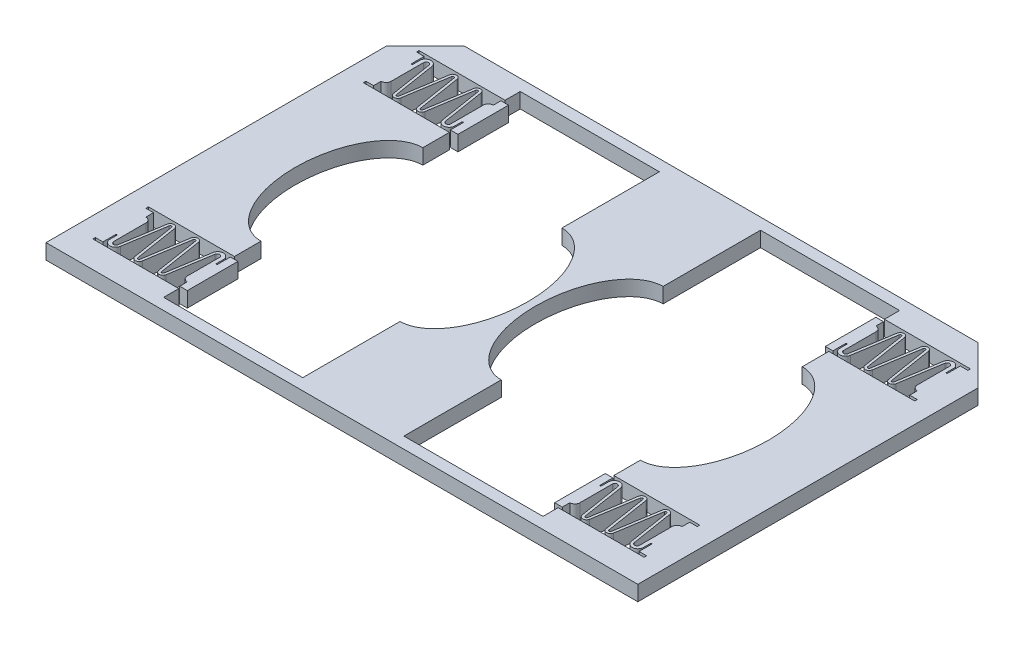
SolidWorks part; units mm, degrees
ref_plane "Front Plane" through (0, 0, 0) normal (0, 0, 1) x (1, 0, 0)
ref_plane "Top Plane" through (0, 0, 0) normal (0, 1, 0) x (1, 0, 0)
ref_plane "Right Plane" through (0, 0, 0) normal (1, 0, 0) x (0, 0, -1)
sketch "Sketch1" plane through (0, 0, 0) normal (0, 1, 0) x (1, 0, 0)
  line L0 (0, 67.25) -> (0, 0)
  line L1 (0, 0) -> (117, 0)
  line L2 (117, 0) -> (117, 67.25)
  line L3 (117, 67.25) -> (109.25, 75)
  line L4 (109.25, 75) -> (7.75, 75)
  line L5 (7.75, 75) -> (0, 67.25)
  line L6 (58.5, 0) -> (58.5, 75) construction
  line L7 (48.5, 2.25) -> (48.5, 0) construction
  line L8 (21, 72.75) -> (48.5, 72.75)
  line L9 (21, 72.75) -> (21, 2.25)
  line L10 (21, 2.25) -> (48.5, 2.25)
  line L11 (48.5, 72.75) -> (48.5, 2.25)
  line L12 (48.5, 72.75) -> (48.5, 75) construction
  line L13 (68.5, 72.75) -> (68.5, 2.25)
  line L14 (96, 2.25) -> (68.5, 2.25)
  line L15 (96, 72.75) -> (96, 2.25)
  line L16 (96, 72.75) -> (68.5, 72.75)
  dimension "D1" = 75
  dimension "D2" = 135
  dimension "D3" = 117
  dimension "D4" = 101.5
  dimension "D5" = 10
  dimension "D6" = 70.5
  dimension "D7" = 27.5
extrude "Boss-Extrude1" add sketch "Sketch1" along normal blind 3
sketch "Sketch3" plane through (0, 3, 0) normal (0, 1, 0) x (1, 0, 0)
  line L0 (96, 69.75) -> (96, 58.75)
  line L1 (58.5, 75) -> (58.5, 0) construction
  line L2 (109.25, 75) -> (7.75, 75) construction
  line L3 (0, 0) -> (117, 0) construction
  line L5 (34.75, 72.75) -> (34.75, 2.25) construction
  line L6 (48.5, 72.75) -> (21, 72.75) construction
  line L7 (21, 2.25) -> (48.5, 2.25) construction
  line L8 (82.25, 72.75) -> (82.25, 2.25) construction
  line L9 (96, 72.75) -> (68.5, 72.75) construction
  line L10 (68.5, 2.25) -> (96, 2.25) construction
  line L11 (21, 72.75) -> (21, 2.25) construction
  line L12 (21, 69.75) -> (4, 69.75)
  line L13 (21, 69.75) -> (21, 58.75)
  line L14 (21, 58.75) -> (4, 58.75)
  line L15 (4, 69.75) -> (4, 58.75)
  line L16 (96, 58.75) -> (113, 58.75)
  line L17 (113, 69.75) -> (113, 58.75)
  line L18 (96, 69.75) -> (113, 69.75)
  line L19 (21, 37.5) -> (96, 37.5) construction
  line L20 (113, 5.25) -> (113, 16.25)
  line L21 (96, 16.25) -> (113, 16.25)
  line L22 (96, 5.25) -> (96, 16.25)
  line L23 (96, 5.25) -> (113, 5.25)
  line L24 (21, 5.25) -> (21, 16.25)
  line L25 (21, 16.25) -> (4, 16.25)
  line L26 (4, 5.25) -> (4, 16.25)
  line L27 (21, 5.25) -> (4, 5.25)
  ellipse E0 centre (21, 37.5) end of major axis (21, 21.5) minor radius 9.25
  ellipse E1 centre (48.5, 37.5) end of major axis (48.5, 53.5) minor radius 9.25
  ellipse E2 centre (68.5, 37.5) end of major axis (68.5, 53.5) minor radius 9.25
  ellipse E3 centre (96, 37.5) end of major axis (96, 53.5) minor radius 9.25
  dimension "D1" = 18.5
  dimension "D2" = 32
  dimension "D3" = 3
  dimension "D4" = 17
  dimension "D5" = 11
extrude "Cut-Extrude3" cut sketch "Sketch3" against normal through all
sketch "Sketch5" plane through (0, 3, 0) normal (0, 1, 0) x (1, 0, 0)
  line L0 (4, 64.25) -> (48.5, 64.25) construction
  line L1 (4, 69.75) -> (4, 58.75) construction
  line L2 (48.5, 53.5) -> (48.5, 72.75) construction
  line L3 (6.5, 61.75) -> (6.5, 68.1439)
  line L4 (4, 69.25) -> (5.5, 69.25)
  line L5 (4, 69.25) -> (4, 59.25)
  line L6 (4, 59.25) -> (5.5, 59.25)
  line L7 (5.5, 69.25) -> (5.5, 66.75)
  line L8 (9.8024, 59.9609) -> (11.1734, 68.6173)
  line L9 (5.75, 68.1242) -> (5.75, 66.75)
  line L10 (7.4938, 68.2221) -> (8.8147, 59.8827)
  line L11 (7.9877, 68.3003) -> (9.3085, 59.9609)
  line L12 (11.6673, 68.5391) -> (10.2962, 59.8827)
  line L13 (12.1611, 68.5391) -> (13.5321, 59.8827)
  line L14 (4, 59.25) -> (48.5, 59.25) construction
  line L15 (5.5, 69.25) -> (48.5, 69.25) construction
  line L16 (12.6549, 68.6173) -> (14.026, 59.9609)
  line L17 (14.5198, 59.9609) -> (15.8909, 68.6173)
  line L18 (16.3847, 68.5391) -> (15.0137, 59.8827)
  line L19 (16.8786, 68.5391) -> (18.1994, 60.1997)
  line L20 (17.3724, 68.6173) -> (18.6933, 60.2779)
  line L21 (19.6871, 66.75) -> (19.6871, 60.3561)
  line L22 (22.1871, 69.25) -> (20.6871, 69.25)
  line L23 (22.1871, 69.25) -> (22.1871, 59.25)
  line L24 (22.1871, 59.25) -> (20.6871, 59.25)
  line L25 (20.6871, 69.25) -> (20.6871, 67.75)
  line L26 (20.4371, 61.75) -> (20.4371, 60.3758)
  line L27 (5.5, 60.75) -> (5.5, 59.25)
  line L28 (20.6871, 61.75) -> (20.6871, 59.25)
  line L29 (58.5, 75) -> (58.5, 0) construction
  line L30 (109.25, 75) -> (7.75, 75) construction
  line L31 (0, 0) -> (117, 0) construction
  line L32 (58.5, 37.5) -> (0, 37.5) construction
  line L33 (0, 67.25) -> (0, 0) construction
  line L34 (58.5, 37.5) -> (117, 37.5) construction
  line L35 (117, 0) -> (117, 67.25) construction
  line L36 (111.5, 69.25) -> (68.5, 69.25) construction
  line L37 (113, 59.25) -> (68.5, 59.25) construction
  line L38 (113, 64.25) -> (68.5, 64.25) construction
  line L39 (96.3129, 61.75) -> (96.3129, 59.25)
  line L40 (111.5, 60.75) -> (111.5, 59.25)
  line L41 (96.5629, 61.75) -> (96.5629, 60.3758)
  line L42 (96.3129, 69.25) -> (96.3129, 67.75)
  line L43 (94.8129, 59.25) -> (96.3129, 59.25)
  line L44 (94.8129, 69.25) -> (94.8129, 59.25)
  line L45 (94.8129, 69.25) -> (96.3129, 69.25)
  line L46 (97.3129, 66.75) -> (97.3129, 60.3561)
  line L47 (99.6276, 68.6173) -> (98.3067, 60.2779)
  line L48 (100.1214, 68.5391) -> (98.8006, 60.1997)
  line L49 (100.6153, 68.5391) -> (101.9863, 59.8827)
  line L50 (102.4802, 59.9609) -> (101.1091, 68.6173)
  line L51 (104.3451, 68.6173) -> (102.974, 59.9609)
  line L52 (104.8389, 68.5391) -> (103.4679, 59.8827)
  line L53 (105.3327, 68.5391) -> (106.7038, 59.8827)
  line L54 (109.0123, 68.3003) -> (107.6915, 59.9609)
  line L55 (109.5062, 68.2221) -> (108.1853, 59.8827)
  line L56 (111.25, 68.1242) -> (111.25, 66.75)
  line L57 (107.1976, 59.9609) -> (105.8266, 68.6173)
  line L58 (111.5, 69.25) -> (111.5, 66.75)
  line L59 (113, 59.25) -> (111.5, 59.25)
  line L60 (113, 69.25) -> (113, 59.25)
  line L61 (113, 69.25) -> (111.5, 69.25)
  line L62 (110.5, 61.75) -> (110.5, 68.1439)
  line L63 (113, 10.75) -> (68.5, 10.75) construction
  line L64 (113, 15.75) -> (68.5, 15.75) construction
  line L65 (111.5, 5.75) -> (68.5, 5.75) construction
  line L66 (110.5, 13.25) -> (110.5, 6.8561)
  line L67 (113, 5.75) -> (111.5, 5.75)
  line L68 (113, 5.75) -> (113, 15.75)
  line L69 (113, 15.75) -> (111.5, 15.75)
  line L70 (111.5, 5.75) -> (111.5, 8.25)
  line L71 (107.1976, 15.0391) -> (105.8266, 6.3827)
  line L72 (111.25, 6.8758) -> (111.25, 8.25)
  line L73 (109.5062, 6.7779) -> (108.1853, 15.1173)
  line L74 (109.0123, 6.6997) -> (107.6915, 15.0391)
  line L75 (105.3327, 6.4609) -> (106.7038, 15.1173)
  line L76 (104.8389, 6.4609) -> (103.4679, 15.1173)
  line L77 (104.3451, 6.3827) -> (102.974, 15.0391)
  line L78 (102.4802, 15.0391) -> (101.1091, 6.3827)
  line L79 (100.6153, 6.4609) -> (101.9863, 15.1173)
  line L80 (100.1214, 6.4609) -> (98.8006, 14.8003)
  line L81 (99.6276, 6.3827) -> (98.3067, 14.7221)
  line L82 (97.3129, 8.25) -> (97.3129, 14.6439)
  line L83 (94.8129, 5.75) -> (96.3129, 5.75)
  line L84 (94.8129, 5.75) -> (94.8129, 15.75)
  line L85 (94.8129, 15.75) -> (96.3129, 15.75)
  line L86 (96.3129, 5.75) -> (96.3129, 7.25)
  line L87 (96.5629, 13.25) -> (96.5629, 14.6242)
  line L88 (111.5, 14.25) -> (111.5, 15.75)
  line L89 (96.3129, 13.25) -> (96.3129, 15.75)
  line L90 (5.5, 5.75) -> (48.5, 5.75) construction
  line L91 (4, 15.75) -> (48.5, 15.75) construction
  line L92 (4, 10.75) -> (48.5, 10.75) construction
  line L93 (20.6871, 13.25) -> (20.6871, 15.75)
  line L94 (5.5, 14.25) -> (5.5, 15.75)
  line L95 (20.4371, 13.25) -> (20.4371, 14.6242)
  line L96 (20.6871, 5.75) -> (20.6871, 7.25)
  line L97 (22.1871, 15.75) -> (20.6871, 15.75)
  line L98 (22.1871, 5.75) -> (22.1871, 15.75)
  line L99 (22.1871, 5.75) -> (20.6871, 5.75)
  line L100 (19.6871, 8.25) -> (19.6871, 14.6439)
  line L101 (17.3724, 6.3827) -> (18.6933, 14.7221)
  line L102 (16.8786, 6.4609) -> (18.1994, 14.8003)
  line L103 (16.3847, 6.4609) -> (15.0137, 15.1173)
  line L104 (14.5198, 15.0391) -> (15.8909, 6.3827)
  line L105 (12.6549, 6.3827) -> (14.026, 15.0391)
  line L106 (12.1611, 6.4609) -> (13.5321, 15.1173)
  line L107 (11.6673, 6.4609) -> (10.2962, 15.1173)
  line L108 (7.9877, 6.6997) -> (9.3085, 15.0391)
  line L109 (7.4938, 6.7779) -> (8.8147, 15.1173)
  line L110 (5.75, 6.8758) -> (5.75, 8.25)
  line L111 (9.8024, 15.0391) -> (11.1734, 6.3827)
  line L112 (5.5, 5.75) -> (5.5, 8.25)
  line L113 (4, 15.75) -> (5.5, 15.75)
  line L114 (4, 5.75) -> (4, 15.75)
  line L115 (4, 5.75) -> (5.5, 5.75)
  line L116 (6.5, 13.25) -> (6.5, 6.8561)
  arc A0 (5.5, 60.75) -> (6.5, 61.75) centre (5.5, 61.75) ccw
  arc A1 (5.5, 66.75) -> (5.75, 66.75) centre (5.625, 66.75) ccw
  arc A4 (9.3085, 59.9609) -> (9.8024, 59.9609) centre (9.5554, 60) ccw
  arc A5 (8.8147, 59.8827) -> (10.2962, 59.8827) centre (9.5554, 60) ccw
  arc A6 (12.1611, 68.5391) -> (11.6673, 68.5391) centre (11.9142, 68.5) ccw
  arc A8 (14.026, 59.9609) -> (14.5198, 59.9609) centre (14.2729, 60) ccw
  arc A9 (13.5321, 59.8827) -> (15.0137, 59.8827) centre (14.2729, 60) ccw
  arc A10 (16.8786, 68.5391) -> (16.3847, 68.5391) centre (16.6316, 68.5) ccw
  arc A12 (20.6871, 67.75) -> (19.6871, 66.75) centre (20.6871, 66.75) ccw
  arc A13 (20.6871, 61.75) -> (20.4371, 61.75) centre (20.5621, 61.75) ccw
  arc A16 (7.9877, 68.3003) -> (5.75, 68.1242) centre (6.8758, 68.1242) ccw
  arc A17 (6.5, 68.1439) -> (7.4938, 68.2221) centre (7, 68.1439) cw
  arc A18 (18.1994, 60.1997) -> (20.4371, 60.3758) centre (19.3113, 60.3758) ccw
  arc A19 (18.6933, 60.2779) -> (19.6871, 60.3561) centre (19.1871, 60.3561) ccw
  arc A20 (12.6549, 68.6173) -> (11.1734, 68.6173) centre (11.9142, 68.5) ccw
  arc A21 (12.6549, 68.6173) -> (11.1734, 68.6173) centre (11.9142, 68.5) ccw
  arc A22 (17.3724, 68.6173) -> (15.8909, 68.6173) centre (16.6316, 68.5) ccw
  arc A23 (99.6276, 68.6173) -> (101.1091, 68.6173) centre (100.3684, 68.5) cw
  arc A24 (104.3451, 68.6173) -> (105.8266, 68.6173) centre (105.0858, 68.5) cw
  arc A25 (104.3451, 68.6173) -> (105.8266, 68.6173) centre (105.0858, 68.5) cw
  arc A26 (98.3067, 60.2779) -> (97.3129, 60.3561) centre (97.8129, 60.3561) cw
  arc A27 (98.8006, 60.1997) -> (96.5629, 60.3758) centre (97.6887, 60.3758) cw
  arc A28 (110.5, 68.1439) -> (109.5062, 68.2221) centre (110, 68.1439) ccw
  arc A29 (109.0123, 68.3003) -> (111.25, 68.1242) centre (110.1242, 68.1242) cw
  arc A30 (96.3129, 61.75) -> (96.5629, 61.75) centre (96.4379, 61.75) cw
  arc A31 (96.3129, 67.75) -> (97.3129, 66.75) centre (96.3129, 66.75) cw
  arc A32 (100.1214, 68.5391) -> (100.6153, 68.5391) centre (100.3684, 68.5) cw
  arc A33 (103.4679, 59.8827) -> (101.9863, 59.8827) centre (102.7271, 60) cw
  arc A34 (102.974, 59.9609) -> (102.4802, 59.9609) centre (102.7271, 60) cw
  arc A35 (104.8389, 68.5391) -> (105.3327, 68.5391) centre (105.0858, 68.5) cw
  arc A36 (108.1853, 59.8827) -> (106.7038, 59.8827) centre (107.4446, 60) cw
  arc A37 (107.6915, 59.9609) -> (107.1976, 59.9609) centre (107.4446, 60) cw
  arc A38 (111.5, 66.75) -> (111.25, 66.75) centre (111.375, 66.75) cw
  arc A39 (111.5, 60.75) -> (110.5, 61.75) centre (111.5, 61.75) cw
  arc A40 (111.5, 14.25) -> (110.5, 13.25) centre (111.5, 13.25) ccw
  arc A41 (111.5, 8.25) -> (111.25, 8.25) centre (111.375, 8.25) ccw
  arc A42 (107.6915, 15.0391) -> (107.1976, 15.0391) centre (107.4446, 15) ccw
  arc A43 (108.1853, 15.1173) -> (106.7038, 15.1173) centre (107.4446, 15) ccw
  arc A44 (104.8389, 6.4609) -> (105.3327, 6.4609) centre (105.0858, 6.5) ccw
  arc A45 (102.974, 15.0391) -> (102.4802, 15.0391) centre (102.7271, 15) ccw
  arc A46 (103.4679, 15.1173) -> (101.9863, 15.1173) centre (102.7271, 15) ccw
  arc A47 (100.1214, 6.4609) -> (100.6153, 6.4609) centre (100.3684, 6.5) ccw
  arc A48 (96.3129, 7.25) -> (97.3129, 8.25) centre (96.3129, 8.25) ccw
  arc A49 (96.3129, 13.25) -> (96.5629, 13.25) centre (96.4379, 13.25) ccw
  arc A50 (109.0123, 6.6997) -> (111.25, 6.8758) centre (110.1242, 6.8758) ccw
  arc A51 (110.5, 6.8561) -> (109.5062, 6.7779) centre (110, 6.8561) cw
  arc A52 (98.8006, 14.8003) -> (96.5629, 14.6242) centre (97.6887, 14.6242) ccw
  arc A53 (98.3067, 14.7221) -> (97.3129, 14.6439) centre (97.8129, 14.6439) ccw
  arc A54 (104.3451, 6.3827) -> (105.8266, 6.3827) centre (105.0858, 6.5) ccw
  arc A55 (104.3451, 6.3827) -> (105.8266, 6.3827) centre (105.0858, 6.5) ccw
  arc A56 (99.6276, 6.3827) -> (101.1091, 6.3827) centre (100.3684, 6.5) ccw
  arc A57 (17.3724, 6.3827) -> (15.8909, 6.3827) centre (16.6316, 6.5) cw
  arc A58 (12.6549, 6.3827) -> (11.1734, 6.3827) centre (11.9142, 6.5) cw
  arc A59 (12.6549, 6.3827) -> (11.1734, 6.3827) centre (11.9142, 6.5) cw
  arc A60 (18.6933, 14.7221) -> (19.6871, 14.6439) centre (19.1871, 14.6439) cw
  arc A61 (18.1994, 14.8003) -> (20.4371, 14.6242) centre (19.3113, 14.6242) cw
  arc A62 (6.5, 6.8561) -> (7.4938, 6.7779) centre (7, 6.8561) ccw
  arc A63 (7.9877, 6.6997) -> (5.75, 6.8758) centre (6.8758, 6.8758) cw
  arc A64 (20.6871, 13.25) -> (20.4371, 13.25) centre (20.5621, 13.25) cw
  arc A65 (20.6871, 7.25) -> (19.6871, 8.25) centre (20.6871, 8.25) cw
  arc A66 (16.8786, 6.4609) -> (16.3847, 6.4609) centre (16.6316, 6.5) cw
  arc A67 (13.5321, 15.1173) -> (15.0137, 15.1173) centre (14.2729, 15) cw
  arc A68 (14.026, 15.0391) -> (14.5198, 15.0391) centre (14.2729, 15) cw
  arc A69 (12.1611, 6.4609) -> (11.6673, 6.4609) centre (11.9142, 6.5) cw
  arc A70 (8.8147, 15.1173) -> (10.2962, 15.1173) centre (9.5554, 15) cw
  arc A71 (9.3085, 15.0391) -> (9.8024, 15.0391) centre (9.5554, 15) cw
  arc A72 (5.5, 8.25) -> (5.75, 8.25) centre (5.625, 8.25) cw
  arc A73 (5.5, 14.25) -> (6.5, 13.25) centre (5.5, 13.25) cw
  point P10 (4, 64.25)
  line M15 (4, 58.75) -> (4, 69.75)
  line M25 (4, 5.25) -> (4, 16.25)
  line M39 (113, 16.25) -> (113, 5.25)
  line M49 (113, 69.75) -> (113, 58.75)
  dimension "D3" = 2
  dimension "D4" = 0.25
  dimension "D5" = 81
  dimension "D6" = 0.5
  dimension "D7" = 81
  dimension "D8" = 0.5
  dimension "D11" = 0.5
  dimension "D9" = 0.5
  dimension "D15" = 0.5
  dimension "D18" = 0.5
  dimension "D24" = 1
  dimension "D27" = 0.25
  dimension "D28" = 2.5
  dimension "D31" = 0.5
  dimension "D33" = 0.5
  dimension "D1" = 10
  dimension "D2" = 1.5
  dimension "D12" = 81
  dimension "D13" = 0.5
  dimension "D16" = 0.5
  dimension "D17" = 81
  dimension "D20" = 0.5
  dimension "D21" = 81
  dimension "D22" = 1.5
  dimension "D23" = 2.5
  dimension "D25" = 2.5
  dimension "D26" = 1
  dimension "D29" = 2.5
  dimension "D30" = 0.5
  dimension "D32" = 0.5
extrude "Boss-Extrude3" add sketch "Sketch5" against normal up to surface (3 mm away) contours L20 A22 L17 A8 L16 A20 L8 A4 L11 A16 L9 A1 L7 L4 L6 L27 A0 L3 A17 L10 A5 L12 A6 L13 A9 L18 A10 L19 A18 L26 A13 L28 L24 L23 L22 L25 A12 L21 A19 M15 | A39 L40 L59 L61 L58 A38 L56 A29 L54 A37 L57 A24 L51 A34 L50 A23 L47 A26 L46 A31 L42 L45 L44 L43 L39 A30 L41 A27 L48 A32 L49 A33 L52 A35 L53 A36 L55 A28 L62 M49 | A73 L94 L113 L115 L112 A72 L110 A63 L108 A71 L111 A58 L105 A68 L104 A57 L101 A60 L100 A65 L96 L99 L98 L97 L93 A64 L95 A61 L102 A66 L103 A67 L106 A69 L107 A70 L109 A62 L116 M25 | L81 A56 L78 A45 L77 A54 L71 A42 L74 A50 L72 A41 L70 L67 L69 L88 A40 L66 A51 L73 A43 L75 A44 L76 A46 L79 A47 L80 A52 L87 A49 L89 L85 L84 L83 L86 A48 L82 A53 M39 up to face at (23.625, 0, -37.5)
